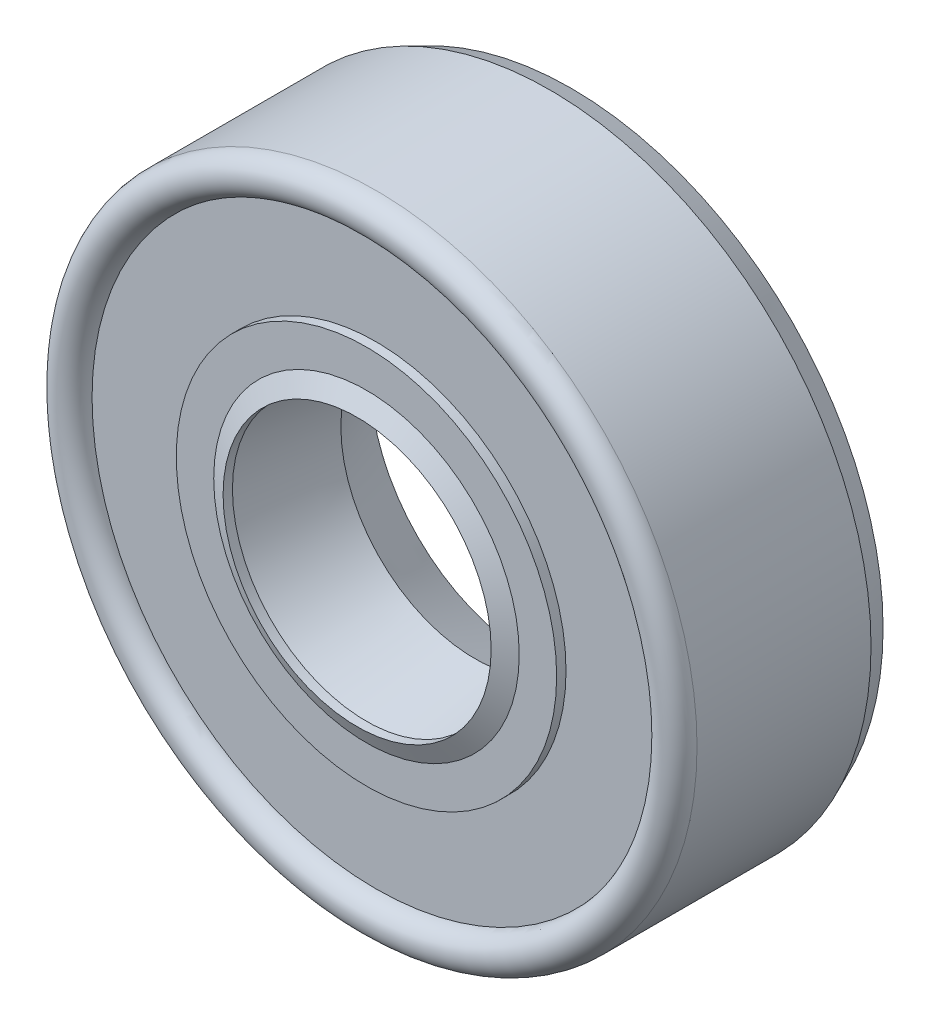
SolidWorks part; units mm, degrees
ref_plane "Front" through (0, 0, 0) normal (0, 0, 1) x (1, 0, 0)
ref_plane "Top" through (0, 0, 0) normal (0, 1, 0) x (1, 0, 0)
ref_plane "Right" through (0, 0, 0) normal (1, 0, 0) x (0, 0, -1)
sketch "Sketch1" plane through (0, 0, 0) normal (1, 0, 0) x (0, 0, -1)
  line L0 (-3.135, 3.9751) -> (-2.8575, 3.9751)
  line L1 (-2.8575, 3.9751) -> (-2.58, 4.5301)
  line L2 (-2.58, 4.5301) -> (0.3575, 3.9751)
  line L3 (0.3575, 3.9751) -> (2.0637, 4.8076)
  line L4 (2.0637, 4.8076) -> (2.0637, 5.0851)
  line L5 (2.0637, 5.0851) -> (0.9125, 5.0851)
  line L6 (-0.1975, 5.0851) -> (-2.025, 5.0851)
  line L7 (-2.025, 5.0851) -> (-2.025, 8.97)
  line L8 (-2.025, 8.97) -> (1.945, 8.97)
  line L9 (1.945, 8.97) -> (1.945, 9.1088)
  line L10 (1.945, 9.1088) -> (2.58, 9.1088)
  line L11 (2.58, 9.1088) -> (2.58, 8.97)
  line L12 (2.58, 8.97) -> (3.215, 8.97)
  line L13 (3.215, 8.97) -> (3.215, 9.2475)
  line L14 (3.215, 9.2475) -> (2.58, 9.525)
  line L15 (2.58, 9.525) -> (-2.58, 9.525)
  line L16 (-2.58, 8.415) -> (-2.58, 5.6401)
  line L17 (-2.58, 5.6401) -> (-2.8575, 5.6401)
  line L18 (-2.8575, 5.6401) -> (-2.8575, 4.5301)
  line L19 (-2.8575, 4.5301) -> (-3.135, 3.9751)
  line L20 (3.135, 0) -> (-3.135, 0) construction
  line L21 (-2.8575, 3.9751) -> (0.3575, 3.9751) construction
  line L22 (0, 9.525) -> (0, 8.97) construction
  line L23 (0, 8.97) -> (0, 8.415) construction
  line L24 (0, 8.415) -> (0, 7.86) construction
  line L25 (0, 7.86) -> (0, 7.305) construction
  line L26 (0, 7.305) -> (0, 6.75) construction
  line L27 (0, 6.75) -> (0, 6.1951) construction
  line L28 (0, 6.1951) -> (0, 5.6401) construction
  line L29 (0, 5.6401) -> (0, 5.0851) construction
  line L30 (0, 5.0851) -> (0, 4.5301) construction
  line L31 (0, 4.5301) -> (0, 3.9751) construction
  line L32 (-3.135, 3.9751) -> (-3.135, 8.97) construction
  line L33 (-3.135, 8.97) -> (-2.58, 8.97) construction
  line L34 (3.215, 8.97) -> (3.215, 3.9751) construction
  line L35 (3.215, 3.9751) -> (0.3575, 3.9751) construction
  line L36 (-3.135, 6.4726) -> (-2.5, 6.4726) construction
  line L37 (-2.5, 6.4726) -> (-1.865, 6.4726) construction
  line L38 (-1.865, 6.4726) -> (-1.23, 6.4726) construction
  line L39 (-1.23, 6.4726) -> (-0.595, 6.4726) construction
  line L40 (-0.595, 6.4726) -> (0.04, 6.4726) construction
  line L41 (0.04, 6.4726) -> (0.675, 6.4726) construction
  line L42 (0.675, 6.4726) -> (1.31, 6.4726) construction
  line L43 (1.31, 6.4726) -> (1.945, 6.4726) construction
  line L44 (1.945, 6.4726) -> (2.58, 6.4726) construction
  line L45 (2.58, 6.4726) -> (3.215, 6.4726) construction
  line L46 (0.3575, 6.4726) -> (0.3575, 5.0851) construction
  line L47 (0.3575, 5.0851) -> (0.3575, 3.9751) construction
  line L48 (2.58, 6.4726) -> (2.58, 8.97) construction
  line L49 (1.945, 8.97) -> (1.945, 6.4726) construction
  line L50 (2.58, 9.525) -> (2.58, 9.1088) construction
  line L51 (0, 8.415) -> (-2.58, 8.415) construction
  line L52 (-2.58, 5.6401) -> (-2.58, 4.5301) construction
  line L53 (2.0637, 5.0851) -> (3.215, 5.0851) construction
  line L54 (-2.8575, 8.97) -> (-2.8575, 5.6401) construction
  line L55 (-2.8575, 5.0851) -> (-2.025, 5.0851) construction
  line L56 (2.58, 9.1088) -> (3.215, 9.1088) construction
  line L57 (-2.025, 7.0275) -> (-2.58, 7.0275) construction
  line L58 (2.0637, 4.8076) -> (0, 4.8076) construction
  line L59 (-2.8575, 4.5301) -> (-2.58, 4.5301) construction
  arc A0 (0.9125, 5.0851) -> (-0.1975, 5.0851) centre (0.3575, 5.0851) ccw construction
  arc A1 (-2.58, 9.525) -> (-2.58, 8.415) centre (-2.58, 8.97) ccw
  arc A2 (-0.1975, 5.0851) -> (0.9125, 5.0851) centre (0.3575, 5.0851) ccw
  dimension "SealWidth" = 6.35
  dimension "SealID" = 7.9502
  dimension "SealOD" = 19.05
revolve "Revolve1" add sketch "Sketch1" angle 360 about L20
sketch "Sketch2" plane through (0, 0, 0) normal (1, 0, 0) x (0, 0, -1)
  line L0 (-3.135, 0) -> (3.135, 0) construction
  line L1 (-3.135, 8.97) -> (-3.135, -8.97) construction
  circle A0 centre (0.3575, 5.0851) radius 0.555
revolve "Revolve2" add sketch "Sketch2" angle 360 about L0
